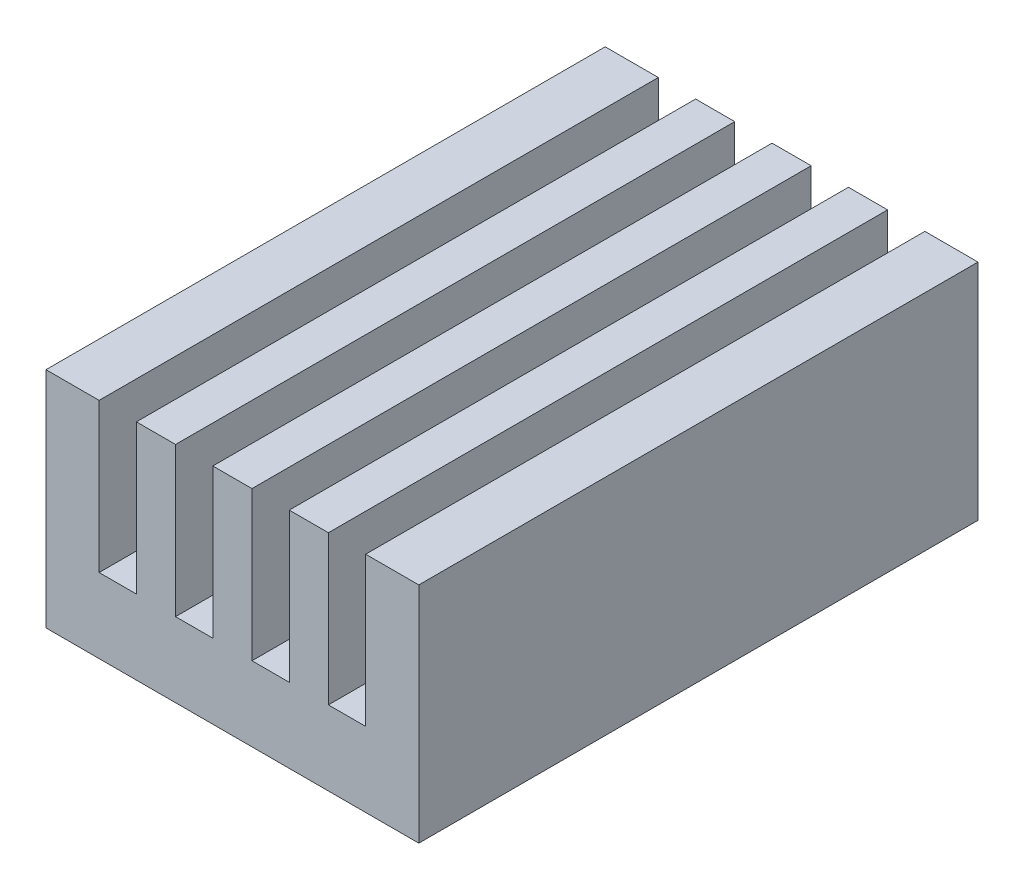
SolidWorks part; units mm, degrees
material "6061-T6 (SS)"
ref_plane "Front Plane" through (0, 0, 0) normal (0, 0, 1) x (1, 0, 0)
ref_plane "Top Plane" through (0, 0, 0) normal (0, 1, 0) x (1, 0, 0)
ref_plane "Right Plane" through (0, 0, 0) normal (1, 0, 0) x (0, 0, -1)
sketch "Sketch1" plane through (0, 0, 0) normal (0, 0, 1) x (1, 0, 0)
  line L0 (-5, 6) -> (-5, 0)
  line L1 (-5, 6) -> (5, 6)
  line L2 (-5, 0) -> (5, 0)
  line L3 (5, 6) -> (5, 0)
  line L4 (-5, 6) -> (5, 0) construction
  line L5 (-5, 0) -> (5, 6) construction
  line L8 (0, 6) -> (0, 0) construction
  line L9 (-0.525, 6) -> (-0.525, 2)
  line L10 (0.525, 6) -> (1.525, 6)
  line L11 (0.525, 6) -> (0.525, 2)
  line L12 (0.525, 2) -> (1.525, 2)
  line L13 (1.525, 6) -> (1.525, 2)
  line L14 (2.575, 6) -> (3.575, 6)
  line L15 (2.575, 6) -> (2.575, 2)
  line L16 (2.575, 2) -> (3.575, 2)
  line L17 (3.575, 6) -> (3.575, 2)
  line L18 (-0.525, 2) -> (-1.525, 2)
  line L19 (-1.525, 6) -> (-1.525, 2)
  line L20 (-2.575, 6) -> (-2.575, 2)
  line L21 (-2.575, 2) -> (-3.575, 2)
  line L22 (-3.575, 6) -> (-3.575, 2)
  point P0 (2.575, -2)
  point P1 (0, 3)
  point P3 (0, 0)
  dimension "D1" = 10
  dimension "D2" = 6
  dimension "D6" = 1
  dimension "D7" = 0.525
  dimension "D8" = 4
  dimension "D9" = 1.05
  dimension "D10" = 1
extrude "Boss-Extrude1" add sketch "Sketch1" along normal blind 15
equation "\"D10@Sketch1\"=\"D6@Sketch1\""
